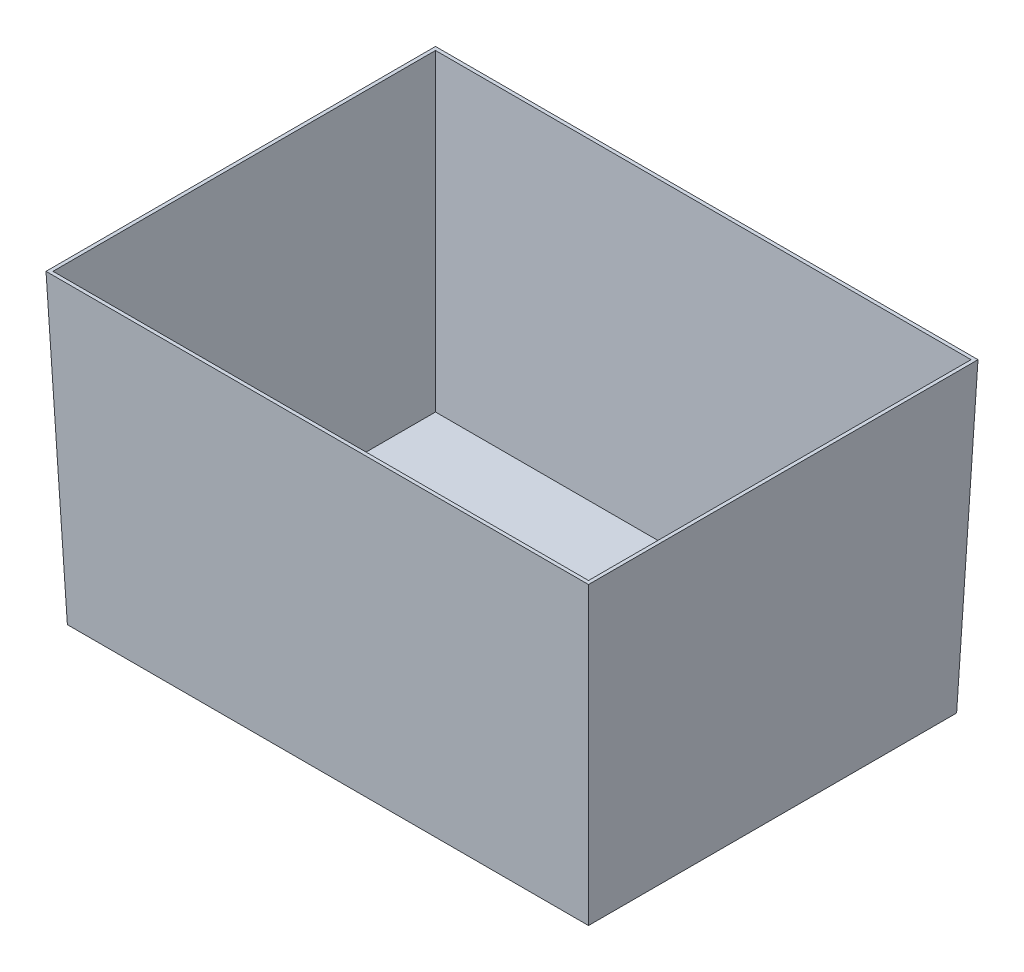
SolidWorks part; units mm, degrees
material "Plástico personalizado"
ref_plane "Alzado" through (0, 0, 0) normal (0, 0, 1) x (1, 0, 0)
ref_plane "Planta" through (0, 0, 0) normal (0, 1, 0) x (1, 0, 0)
ref_plane "Vista lateral" through (0, 0, 0) normal (1, 0, 0) x (0, 0, -1)
sketch "Sketch1" plane through (0, 0, 0) normal (0, 1, 0) x (1, 0, 0)
  line L1 (-390, -280) -> (390, -280)
  line L2 (-390, -280) -> (-390, 280)
  line L3 (-390, 280) -> (390, 280)
  line L4 (390, -280) -> (390, 280)
  line L5 (-390, -280) -> (390, 280) construction
  line L6 (-390, 280) -> (390, -280) construction
  point P0 (0, 0)
  dimension "D1" = 780
  dimension "D2" = 560
extrude "Extrude1" add sketch "Sketch1" against normal blind 440 draft 2
shell "Shell1" thickness 5
